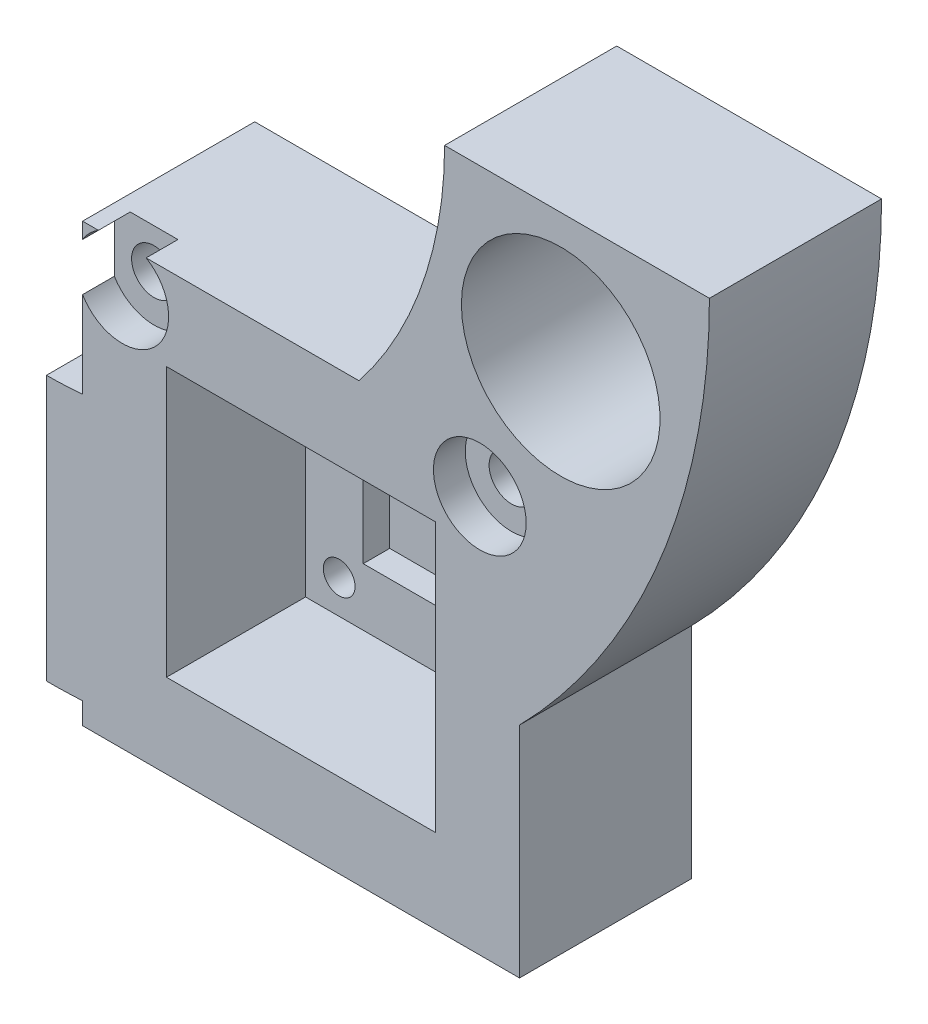
SolidWorks part; units mm, degrees
ref_plane "Plan de face" through (0, 0, 0) normal (0, 0, 1) x (1, 0, 0)
ref_plane "Plan de dessus" through (0, 0, 0) normal (0, 1, 0) x (1, 0, 0)
ref_plane "Plan de droite" through (0, 0, 0) normal (1, 0, 0) x (0, 0, -1)
sketch "Esquisse1" plane through (0, 0, 0) normal (0, 0, 1) x (1, 0, 0)
  line L0 (-16.5, 16.5) -> (16.5, -16.5) construction
  line L1 (-16.5, 16.5) -> (16.5, 16.5)
  line L2 (-16.5, 16.5) -> (-16.5, -16.5)
  line L3 (-16.5, -16.5) -> (16.5, -16.5)
  line L4 (16.5, 16.5) -> (16.5, -16.5)
  line L5 (-16.5, -16.5) -> (16.5, 16.5) construction
  line L11 (10.6664, -10.6664) -> (-10.6664, 10.6664) construction
  line L12 (10.6664, 10.6664) -> (-10.6664, -10.6664) construction
  point P4 (0, 0)
  point P5 (0, 0)
  dimension "D1" = 33
  dimension "D2" = 33
  dimension "D3" = 16.5
  dimension "D4" = 16.5
extrude "Boss.-Extru.1" add sketch "Esquisse1" along normal blind 13
sketch "Esquisse2" plane through (0, 0, 13) normal (0, 0, 1) x (1, 0, 0)
  line L0 (-16.5, 16.5) -> (16.5, -16.5) construction
  line L1 (-16.5, -16.5) -> (16.5, 16.5) construction
  line L2 (-10.16, 0) -> (10.16, 0) construction
  line L3 (10.16, -10.16) -> (-10.16, -10.16) construction
  line L4 (-16.5, 16.5) -> (-16.5, -16.5)
  line L5 (-16.5, -16.5) -> (16.5, -16.5)
  line L6 (16.5, -16.5) -> (16.5, 16.5)
  line L7 (16.5, 16.5) -> (-16.5, 16.5)
  line L8 (-16.5, 16.5) -> (-16.5, -16.5)
  line L9 (-16.5, -16.5) -> (16.5, -16.5)
  line L10 (16.5, -16.5) -> (16.5, 16.5)
  line L11 (16.5, 16.5) -> (-16.5, 16.5)
  line L12 (10.16, -10.16) -> (10.16, 10.16) construction
  line L13 (10.16, 10.16) -> (-10.16, 10.16) construction
  line L14 (-10.16, -10.16) -> (-10.16, 10.16) construction
  line L15 (10.16, -10.16) -> (-10.16, 10.16) construction
  line L16 (10.16, 10.16) -> (-10.16, -10.16) construction
  line L17 (10.16, -10.16) -> (-10.16, -10.16)
  line L18 (10.16, -10.16) -> (10.16, 10.16)
  line L19 (10.16, 10.16) -> (-10.16, 10.16)
  line L20 (-10.16, -10.16) -> (-10.16, 10.16)
  line L21 (10.16, -10.16) -> (-10.16, 10.16) construction
  line L22 (10.16, 10.16) -> (-10.16, -10.16) construction
  line L23 (-7.62, 8.82) -> (7.62, 8.82)
  line L24 (7.62, 8.82) -> (7.62, 6.42)
  line L25 (7.62, 6.42) -> (-7.62, 6.42)
  circle A0 centre (-7.62, 7.62) radius 1.2
  circle A1 centre (7.62, 7.62) radius 1.2
  circle A2 centre (7.62, -7.62) radius 1.2
  circle A3 centre (-7.62, -7.62) radius 1.2
  point P2 (0, 0)
  point P10 (7.62, 7.62)
  point P11 (-7.62, 7.62)
  point P16 (0, 0)
  dimension "D8" = 2.4
  dimension "D9" = 2.4
  dimension "D10" = 2.4
  dimension "D2" = 20.32
  dimension "D3" = 20.32
  dimension "D4" = 2.54
  dimension "D5" = 2.54
  dimension "D6" = 2.54
  dimension "D7" = 2.54
  dimension "D1" = 0
sketch "Esquisse3" plane through (0, 0, 13) normal (0, 0, 1) x (1, 0, 0)
  line L0 (-0.95, 1.7) -> (1.45, -1.7) construction
  line L1 (-4.02, 1.4) -> (-1.92, 1.4)
  line L2 (-4.02, 1.4) -> (-4.02, -1.4)
  line L3 (-4.02, -1.4) -> (-1.92, -1.4)
  line L4 (-1.92, 1.4) -> (-1.92, -1.4)
  line L5 (-0.95, 1.7) -> (1.45, 1.7)
  line L6 (-0.95, 1.7) -> (-0.95, -1.7)
  line L7 (-0.95, -1.7) -> (1.45, -1.7)
  line L8 (1.45, 1.7) -> (1.45, -1.7)
  line L9 (-0.95, -1.7) -> (1.45, 1.7) construction
  line L10 (-4.02, 1.4) -> (-1.92, -1.4) construction
  line L11 (-4.02, -1.4) -> (-1.92, 1.4) construction
  line L12 (10.16, -10.16) -> (10.16, 10.16) construction
  circle A0 centre (0.25, 0) radius 2
  point P8 (0.25, 0)
  point P9 (-2.97, 0)
  dimension "D7" = 4
  dimension "D1" = 3.22
  dimension "D2" = 9.91
  dimension "D3" = 2.8
  dimension "D4" = 2.1
  dimension "D5" = 3.4
  dimension "D6" = 2.4
extrude "Enlèv. mat.-Extru.1" cut sketch "Esquisse3" against normal through all contours L1 L4 L3 L2 | A0
sketch "Esquisse4" plane through (0, 0, 13) normal (0, 0, 1) x (1, 0, 0)
  line L0 (-16.5, 16.5) -> (16.5, -16.5) construction
  line L1 (5.8031, -5.8031) -> (-5.8031, -5.8031)
  line L2 (5.8031, -5.8031) -> (5.8031, 5.8031)
  line L3 (5.8031, 5.8031) -> (-5.8031, 5.8031)
  line L4 (-5.8031, -5.8031) -> (-5.8031, 5.8031)
  line L5 (5.8031, -5.8031) -> (-5.8031, 5.8031) construction
  line L6 (5.8031, 5.8031) -> (-5.8031, -5.8031) construction
  circle A0 centre (0.25, 0) radius 2 construction
  circle A1 centre (0.25, 0) radius 2
  point P0 (0, 0)
  dimension "D1" = 0.25
extrude "Enlèv. mat.-Extru.2" cut sketch "Esquisse4" against normal blind 12.5
extrude "Enlèv. mat.-Extru.3" cut sketch "Esquisse2" against normal through all contours A3 | A2 | A1 L23 A0 L25 | L24 A1
sketch "Esquisse5" plane through (0, 0, 13) normal (0, 0, 1) x (1, 0, 0)
  line L1 (10.16, -10.16) -> (-10.16, -10.16)
  line L2 (10.16, -10.16) -> (10.16, 10.16)
  line L3 (10.16, 10.16) -> (-10.16, 10.16)
  line L4 (-16.5, 16.5) -> (-16.5, -16.5)
  line L5 (-16.5, -16.5) -> (16.5, -16.5)
  line L6 (16.5, -16.5) -> (16.5, 16.5)
  line L7 (16.5, 16.5) -> (-16.5, 16.5)
  line L8 (-16.5, 16.5) -> (-16.5, -16.5)
  line L9 (-16.5, -16.5) -> (16.5, -16.5)
  line L10 (16.5, -16.5) -> (16.5, 16.5)
  line L11 (16.5, 16.5) -> (-16.5, 16.5)
  line L12 (-10.16, -10.16) -> (-10.16, 10.16)
  line L13 (10.16, -10.16) -> (-10.16, 10.16) construction
  line L14 (10.16, 10.16) -> (-10.16, -10.16) construction
  point P2 (0, 0)
  dimension "D2" = 20.32
  dimension "D3" = 20.32
  dimension "D1" = 0
extrude "Enlèv. mat.-Extru.5" cut sketch "Esquisse5" against normal blind 10.5 contours L3 L12 L1 L2
sketch "Esquisse6" plane through (0, 0, 13) normal (0, 0, 1) x (1, 0, 0)
  line L0 (10.16, 0) -> (-10.16, 0) construction
  line L1 (10.16, -10.16) -> (10.16, 10.16) construction
  line L2 (-10.16, -10.16) -> (-10.16, 10.16) construction
  line L3 (-16.5, 0) -> (16.5, 0) construction
  line L4 (-16.5, 16.5) -> (-16.5, -16.5)
  line L5 (-16.5, -16.5) -> (16.5, -16.5)
  line L6 (16.5, -16.5) -> (16.5, 16.5)
  line L7 (16.5, 16.5) -> (-16.5, 16.5)
  line L8 (-16.5, 16.5) -> (-16.5, -16.5)
  line L9 (-16.5, -16.5) -> (16.5, -16.5)
  line L10 (16.5, -16.5) -> (16.5, 16.5)
  line L11 (16.5, 16.5) -> (-16.5, 16.5)
  circle A0 centre (13.5, -13.5) radius 1.5
  circle A1 centre (-13.5, -13.5) radius 1.5
  circle A4 centre (13.5, 13.5) radius 1.5
  circle A5 centre (-13.5, 13.5) radius 1.5
  point P21 (-13.5, 13.5)
  point P22 (13.5, 13.5)
  dimension "D6" = 3
  dimension "D7" = 3
  dimension "D2" = 3
  dimension "D3" = 3
  dimension "D4" = 3
  dimension "D5" = 3
  dimension "D1" = 0
sketch "Esquisse8" plane through (0, 0, 0) normal (0, 0, -1) x (-1, 0, 0)
  line L0 (19.2287, 35.1264) -> (19.2287, -14.9435)
  line L1 (19.2287, 35.1264) -> (27.9232, -14.1828)
  line L2 (19.2287, 35.1264) -> (-30.8412, 35.1264)
  line L3 (14.2287, 30.1264) -> (-19.6098, 25.3707) construction
  circle A0 centre (19.2287, 35.1264) radius 40.045 construction
  circle A1 centre (19.2287, 35.1264) radius 30.0698
  circle A2 centre (19.2287, 35.1264) radius 50.0698
  circle A3 centre (-19.6098, 25.3707) radius 7.5
  point P5 (14.2287, 30.1264)
  line M19 (16.5, -16.5) -> (16.5, 16.5)
  line M20 (16.5, 16.5) -> (-16.5, 16.5)
  line M21 (-16.5, 16.5) -> (-16.5, -16.5)
  dimension "D1" = 80.09
  dimension "D2" = 20
  dimension "D5" = 5
  dimension "D3" = 10
  dimension "D4" = 90
  dimension "D6" = 5
  dimension "D7" = 8
extrude "Boss.-Extru.4" add sketch "Esquisse8" against normal blind 13 contours A2 L0 A1 M19 | L2 A2 A1 A3 M21 M20
hole_wizard "Chambrage pour vis à tête ronde bombée M31" positions "Esquisse3D1" profile "Esquisse7" counterbore size "M3" standard "Ansi Metric" end condition through all
sketch3d "Esquisse3D1"
  point P0 (-13.5, 13.5, 13)
  point P3 (13.5, 13.5, 13)
sketch "Esquisse7" plane through (-13.5, 13.5, 13) normal (1, 0, 0) x (0, -1, 0)
  line L0 (0, 0) -> (0, 13)
  line L1 (0, 13) -> (1.7, 13)
  line L3 (1.7, 13) -> (1.7, 2.4)
  line L4 (1.7, 2.4) -> (3.5, 2.4)
  line L5 (3.5, 2.4) -> (3.5, 0)
  line L7 (3.5, 0) -> (0, 0)
  line L11 (0, -6.35) -> (0, 107.95) construction
  dimension "Diamètre du perçage jusqu'au prochain" = 3.4
  dimension "Profondeur du perçage jusqu'au prochain" = 13
  dimension "Diamètre du chambrage" = 7
  dimension "Profondeur du chambrage" = 2.4
